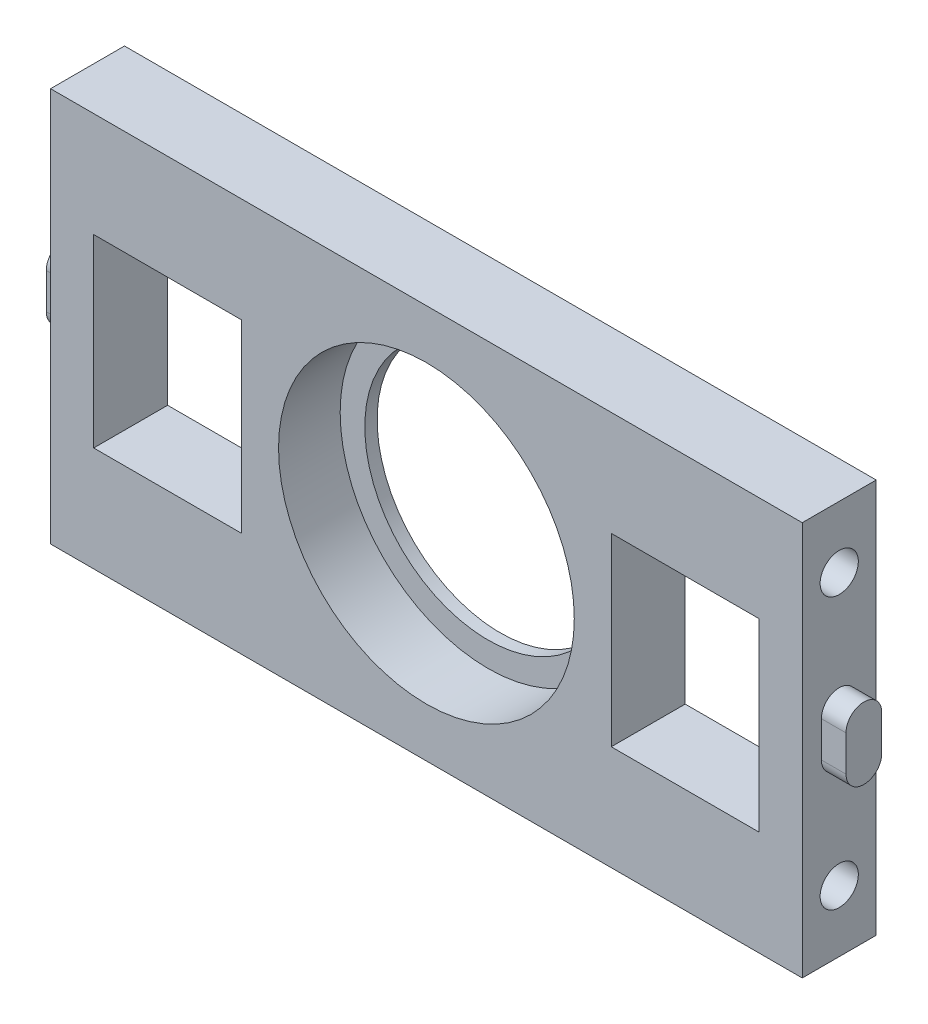
SolidWorks part; units mm, degrees
ref_plane "Спереди" through (0, 0, 0) normal (0, 0, 1) x (1, 0, 0)
ref_plane "Сверху" through (0, 0, 0) normal (0, 1, 0) x (1, 0, 0)
ref_plane "Справа" through (0, 0, 0) normal (1, 0, 0) x (0, 0, -1)
sketch "Эскиз1" plane through (0, 0, 0) normal (0, 0, 1) x (1, 0, 0)
  line L1 (-30.5, 16) -> (30.5, 16)
  line L2 (-30.5, 16) -> (-30.5, -16)
  line L3 (-30.5, -16) -> (30.5, -16)
  line L4 (30.5, 16) -> (30.5, -16)
  line L5 (-30.5, 16) -> (30.5, -16) construction
  line L6 (-30.5, -16) -> (30.5, 16) construction
  circle A0 centre (0, 0) radius 10
  circle A1 centre (0, 0) radius 12
  point P0 (0, 0)
  dimension "D3" = 20
  dimension "D4" = 24
  dimension "D1" = 32
  dimension "D2" = 61
extrude "Бобышка-Вытянуть1" add sketch "Эскиз1" along normal blind 6 contours L1 L4 L3 L2
sketch "Эскиз2" plane through (0, 0, 6) normal (0, 0, 1) x (1, 0, 0)
  circle A0 centre (0, 0) radius 10
  dimension "D1" = 20
extrude "Вырез-Вытянуть13" cut sketch "Эскиз2" against normal blind 6
sketch "Эскиз4" plane through (0, 0, 6) normal (0, 0, 1) x (1, 0, 0)
  circle A0 centre (0, 0) radius 12
extrude "Вырез-Вытянуть14" cut sketch "Эскиз4" against normal blind 5
sketch "Эскиз5" plane through (0, 0, 6) normal (0, 0, 1) x (1, 0, 0)
  line L0 (7.1913, 1.253) -> (19.1913, -13.747)
  line L1 (-15, -7.5) -> (-27, -7.5)
  line L2 (-15, -7.5) -> (-15, 7.5)
  line L3 (-15, 7.5) -> (-27, 7.5)
  line L4 (-27, -7.5) -> (-27, 7.5)
  line L5 (-15, -7.5) -> (-27, 7.5) construction
  line L6 (-15, 7.5) -> (-27, -7.5) construction
  line L7 (15, 7.5) -> (27, 7.5)
  line L8 (15, 7.5) -> (15, -7.5)
  line L9 (15, -7.5) -> (27, -7.5)
  line L10 (27, 7.5) -> (27, -7.5)
  line L11 (15, 7.5) -> (27, -7.5) construction
  line L12 (15, -7.5) -> (27, 7.5) construction
  line L13 (22.8087, 13.747) -> (34.8087, -1.253)
  line L14 (-7.1913, -1.253) -> (-19.1913, 13.747)
  line L15 (-22.8087, -13.747) -> (-34.8087, 1.253)
  point P0 (-21, 0)
  point P5 (21, 0)
  dimension "D1" = 12
  dimension "D2" = 15
  dimension "D3" = 12
  dimension "D4" = 15
  dimension "D5" = 10
  dimension "D6" = 10
  dimension "D7" = 10
  dimension "D8" = 10
extrude "Вырез-Вытянуть16" cut sketch "Эскиз5" against normal blind 6 contours L10 L7 L8 L9 | L4 L1 L2 L3
sketch "Эскиз8" plane through (-30.5, 0, 0) normal (-1, 0, 0) x (0, 0, 1)
  line L0 (2.9, -1.5) -> (2.9, 1.4) construction
  line L1 (1.45, -1.5) -> (1.45, 1.4)
  line L2 (4.35, -1.5) -> (4.35, 1.4)
  arc A0 (1.45, -1.5) -> (4.35, -1.5) centre (2.9, -1.5) ccw
  arc A1 (4.35, 1.4) -> (1.45, 1.4) centre (2.9, 1.4) ccw
  point P2 (2.9, -0.05)
extrude "Бобышка-Вытянуть12" add sketch "Эскиз8" along normal blind 2
sketch "Эскиз9" plane through (30.5, 0, 0) normal (1, 0, 0) x (0, 0, -1)
  line L0 (-3, 1.45) -> (-3, -1.45) construction
  line L1 (-1.55, 1.45) -> (-1.55, -1.45)
  line L2 (-4.45, 1.45) -> (-4.45, -1.45)
  arc A0 (-1.55, 1.45) -> (-4.45, 1.45) centre (-3, 1.45) ccw
  arc A1 (-4.45, -1.45) -> (-1.55, -1.45) centre (-3, -1.45) ccw
  point P2 (-3, 0)
extrude "Бобышка-Вытянуть13" add sketch "Эскиз9" along normal blind 2
sketch "Эскиз10" plane through (-30.5, 0, 0) normal (-1, 0, 0) x (0, 0, 1)
  circle A0 centre (3, 10) radius 1.55
  circle A1 centre (3, -11) radius 1.55
  dimension "D1" = 3.1
  dimension "D2" = 3.1
extrude "Вырез-Вытянуть18" cut sketch "Эскиз10" against normal blind 15
sketch "Эскиз11" plane through (30.5, 0, 0) normal (1, 0, 0) x (0, 0, -1)
  circle A0 centre (-3, 11) radius 1.55
  circle A1 centre (-3, -11) radius 1.55
  dimension "D1" = 3.1
extrude "Вырез-Вытянуть19" cut sketch "Эскиз11" against normal blind 15
